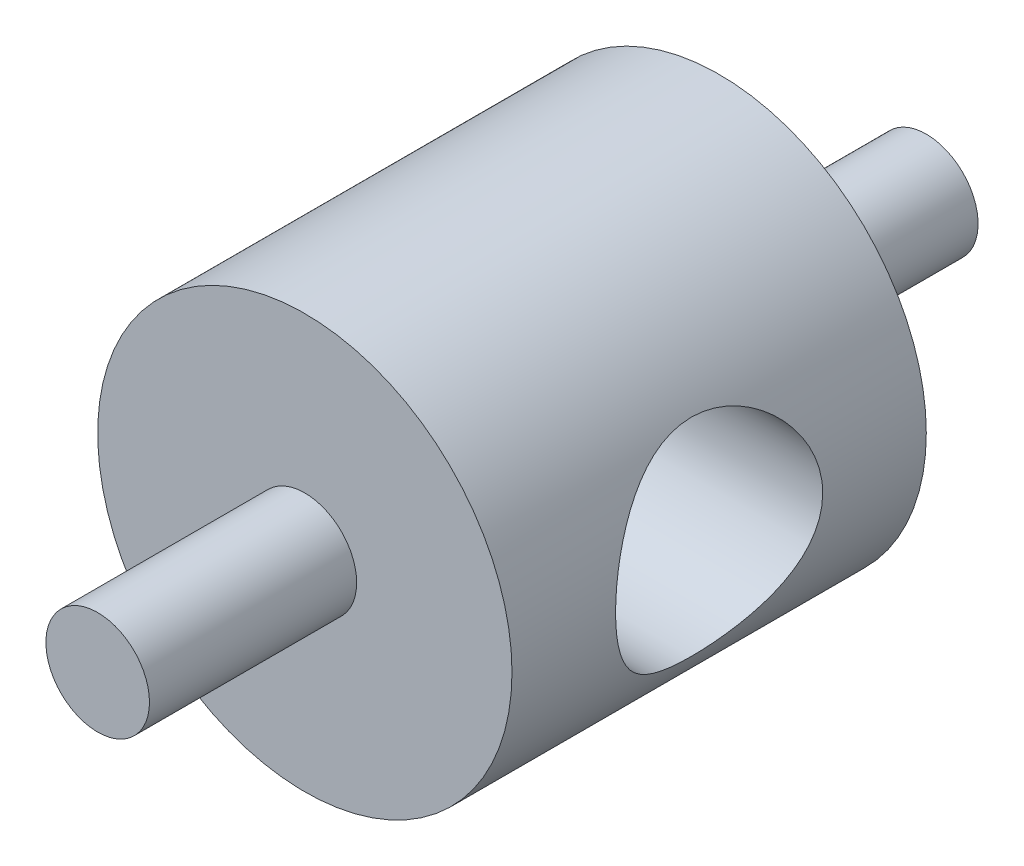
SolidWorks part; units mm, degrees
ref_plane "Front Plane" through (0, 0, 0) normal (0, 0, 1) x (1, 0, 0)
ref_plane "Top Plane" through (0, 0, 0) normal (0, 1, 0) x (1, 0, 0)
ref_plane "Right Plane" through (0, 0, 0) normal (1, 0, 0) x (0, 0, -1)
sketch "Sketch1" plane through (0, 0, 0) normal (0, 0, 1) x (1, 0, 0)
  circle A0 centre (0, 0) radius 6.35
  dimension "D1" = 12.7
extrude "Extrude1" add sketch "Sketch1" along normal blind 6.35 and the other way blind 6.35
sketch "Sketch2" plane through (0, 0, 0) normal (1, 0, 0) x (0, 0, -1)
  circle A0 centre (0, 0) radius 3.175
  dimension "D1" = 6.35
extrude "Cut-Extrude1" cut sketch "Sketch2" against normal up to next and the other way up to next
sketch "Sketch3" plane through (0, 0, 6.35) normal (0, 0, 1) x (1, 0, 0)
  circle A0 centre (0, 0) radius 1.5875
  dimension "D1" = 3.175
extrude "Extrude2" add sketch "Sketch3" along normal blind 6.35 and the other way blind 3.175
sketch "Sketch4" plane through (0, 0, -6.35) normal (0, 0, -1) x (-1, 0, 0)
  circle A0 centre (0, 0) radius 1.5875 construction
  circle A1 centre (0, 0) radius 1.5875
extrude "Extrude3" add sketch "Sketch4" along normal blind 6.35 and the other way blind 3.175
